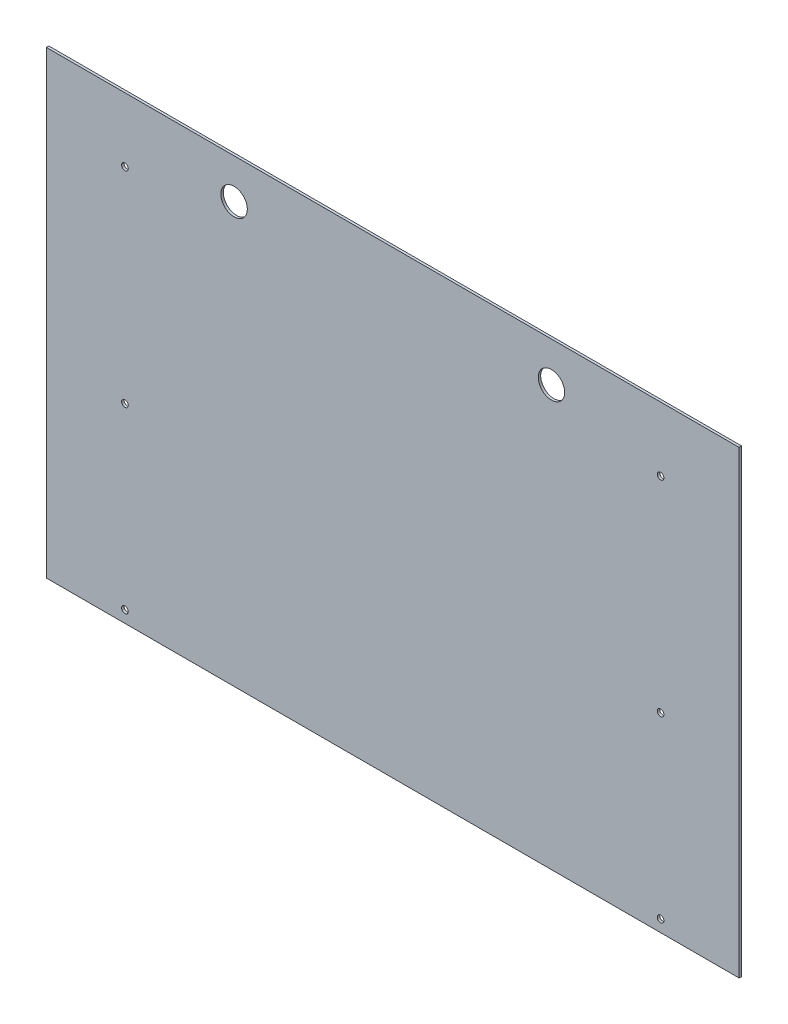
SolidWorks part; units mm, degrees
material "Perspex (TM) GS Acrylic Cast Sheet"
ref_plane "Front Plane" through (0, 0, 0) normal (0, 0, 1) x (1, 0, 0)
ref_plane "Top Plane" through (0, 0, 0) normal (0, 1, 0) x (1, 0, 0)
ref_plane "Right Plane" through (0, 0, 0) normal (1, 0, 0) x (0, 0, -1)
sketch "Sketch1" plane through (0, 0, 0) normal (0, 0, 1) x (1, 0, 0)
  line L0 (665.1625, 1079.5) -> (665.1625, 196.85) construction
  line L1 (-665.1625, 1079.5) -> (665.1625, 1079.5)
  line L2 (-665.1625, 1079.5) -> (-665.1625, 196.85)
  line L3 (-665.1625, 196.85) -> (665.1625, 196.85)
  line L4 (665.1625, 1079.5) -> (665.1625, 196.85)
  line L5 (660.4, 196.85) -> (-660.4, 196.85) construction
  line L10 (0, 0) -> (0, 1079.5) construction
  line L11 (488.95, 1117.6) -> (539.75, 1117.6) construction
  dimension "D1" = 38.1
extrude "Extrude1" add sketch "Sketch1" along normal blind 4.7625
sketch "Sketch2" plane through (0, 0, 4.7625) normal (0, 0, 1) x (1, 0, 0)
  line L0 (514.35, 958.85) -> (514.35, 956.31) construction
  line L3 (514.35, 565.15) -> (514.35, 562.61) construction
  line L4 (514.35, 222.25) -> (514.35, 219.71) construction
  line L5 (0, 0) -> (0, 1473.4644) construction
  line L6 (0, 0) -> (0, 1517.5653) construction
  line L7 (-514.35, 222.25) -> (-514.35, 219.71) construction
  line L8 (-514.35, 565.15) -> (-514.35, 562.61) construction
  line L9 (-514.35, 958.85) -> (-514.35, 956.31) construction
  circle A0 centre (514.35, 956.31) radius 6.35
  circle A2 centre (514.35, 958.85) radius 6.35 construction
  circle A4 centre (514.35, 562.61) radius 6.35
  circle A6 centre (514.35, 219.71) radius 6.35
  circle A7 centre (-514.35, 219.71) radius 6.35
  circle A8 centre (-514.35, 562.61) radius 6.35
  circle A9 centre (-514.35, 956.31) radius 6.35
  dimension "D1" = 2.54
extrude "Cut-Extrude1" cut sketch "Sketch2" against normal through all
sketch "Sketch3" plane through (0, 0, 4.7625) normal (0, 0, 1) x (1, 0, 0)
  line L0 (0, 1079.5) -> (0, 600.0109) construction
  line L1 (665.1625, 1079.5) -> (-665.1625, 1079.5) construction
  circle A0 centre (304.8, 1003.3) radius 25.4
  circle A1 centre (-304.8, 1003.3) radius 25.4
  dimension "D3" = 50.8
  dimension "D1" = 609.6
  dimension "D2" = 76.2
extrude "Cut-Extrude2" cut sketch "Sketch3" against normal through all
